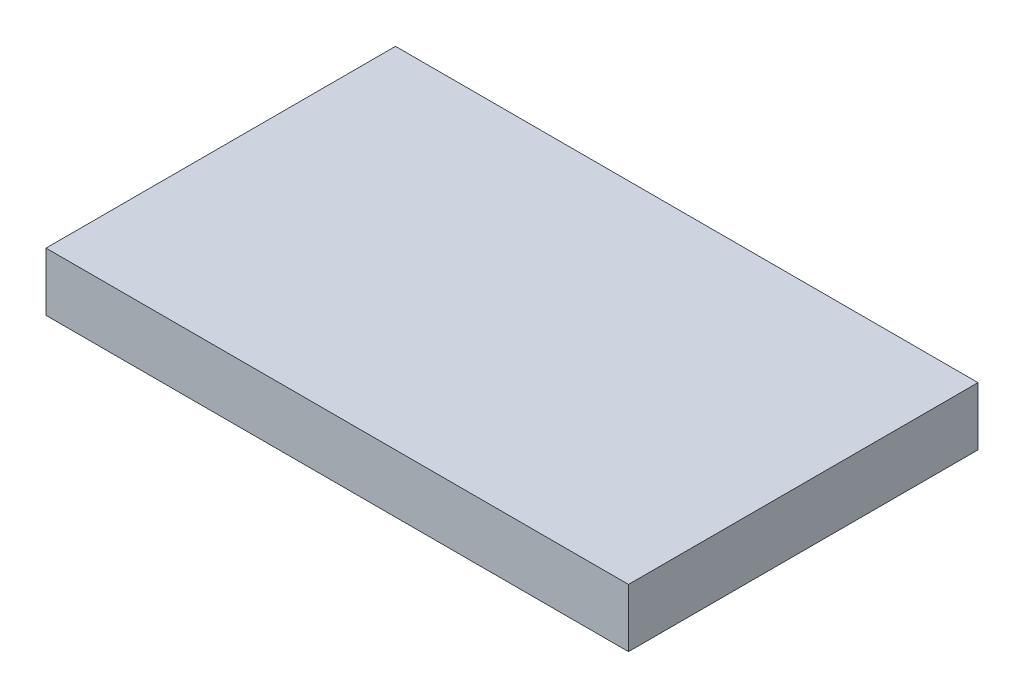
SolidWorks part; units mm, degrees
ref_plane "Front Plane" through (0, 0, 0) normal (0, 0, 1) x (1, 0, 0)
ref_plane "Top Plane" through (0, 0, 0) normal (0, 1, 0) x (1, 0, 0)
ref_plane "Right Plane" through (0, 0, 0) normal (1, 0, 0) x (0, 0, -1)
sketch "Sketch1" plane through (0, 0, 0) normal (0, 1, 0) x (1, 0, 0)
  line L1 (-50, -30) -> (50, -30)
  line L2 (-50, -30) -> (-50, 30)
  line L3 (-50, 30) -> (50, 30)
  line L4 (50, -30) -> (50, 30)
  line L5 (-50, -30) -> (50, 30) construction
  line L6 (-50, 30) -> (50, -30) construction
  point P0 (0, 0)
  dimension "D1" = 100
  dimension "D2" = 60
extrude "Boss-Extrude1" add sketch "Sketch1" along normal blind 10
